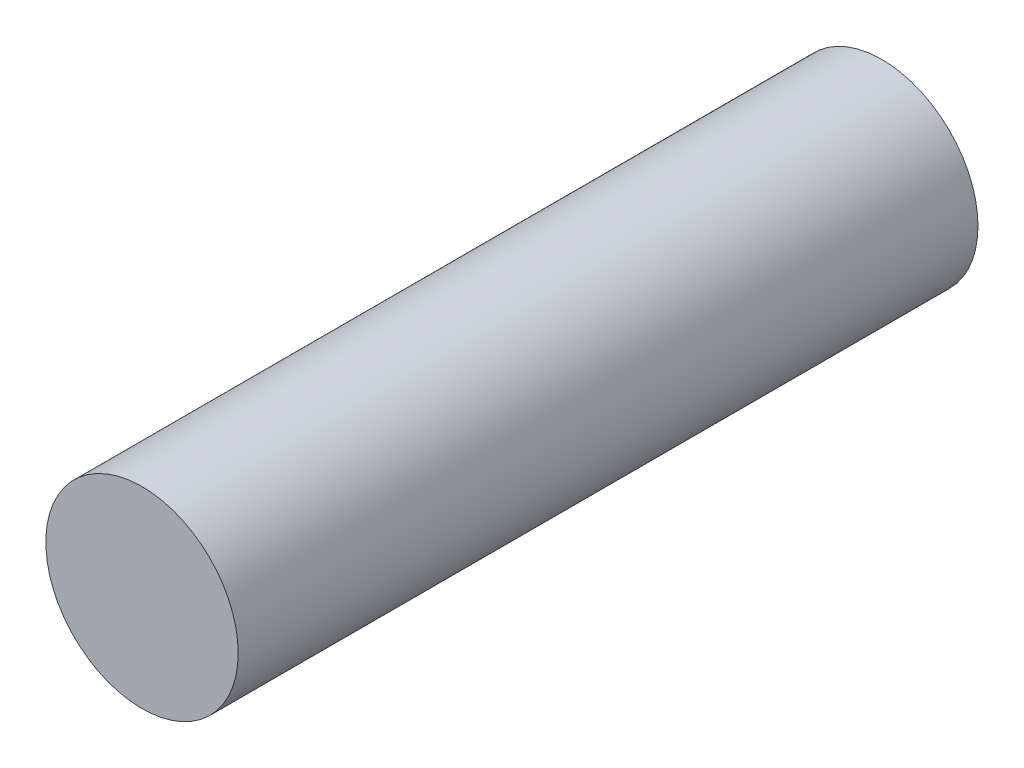
SolidWorks part; units mm, degrees
ref_plane "Ön Düzlem" through (0, 0, 0) normal (0, 0, 1) x (1, 0, 0)
ref_plane "Üst Düzlem" through (0, 0, 0) normal (0, 1, 0) x (1, 0, 0)
ref_plane "Sağ Düzlem" through (0, 0, 0) normal (1, 0, 0) x (0, 0, -1)
sketch "Çizim1" plane through (0, 0, 0) normal (0, 0, 1) x (1, 0, 0)
  circle A0 centre (0, 0) radius 13
  dimension "D1" = 26
extrude "Yükseklik-Ekstrüzyon1" add sketch "Çizim1" along normal blind 100
